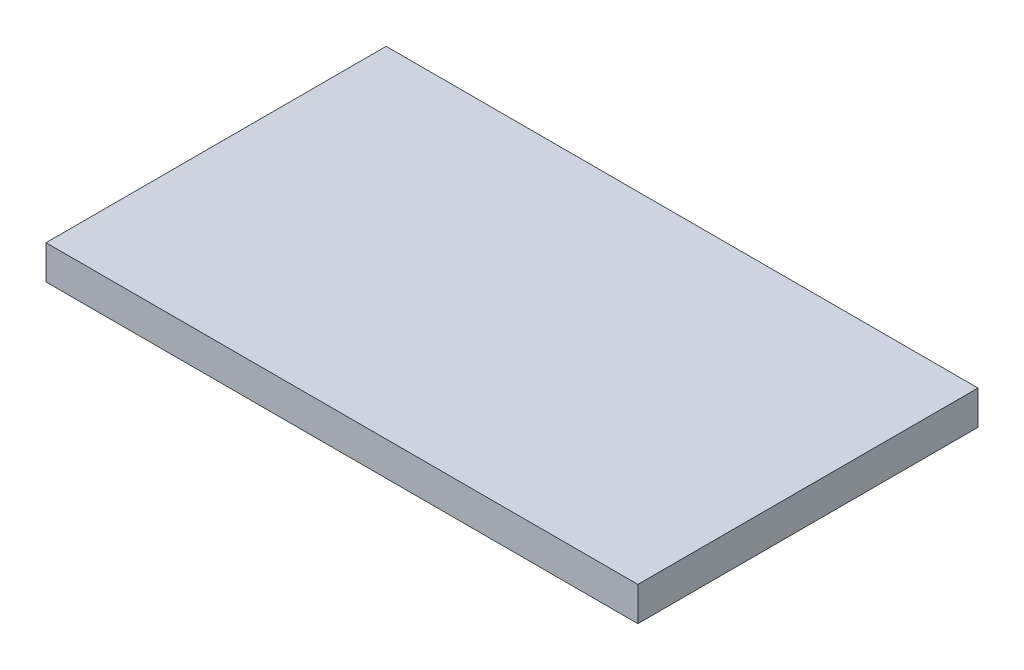
SolidWorks part; units mm, degrees
ref_plane "Front Plane" through (0, 0, 0) normal (0, 0, 1) x (1, 0, 0)
ref_plane "Top Plane" through (0, 0, 0) normal (0, 1, 0) x (1, 0, 0)
ref_plane "Right Plane" through (0, 0, 0) normal (1, 0, 0) x (0, 0, -1)
sketch "Sketch1" plane through (0, 0, 0) normal (0, 1, 0) x (1, 0, 0)
  line L1 (-43.5, 25) -> (43.5, 25)
  line L2 (-43.5, 25) -> (-43.5, -25)
  line L3 (-43.5, -25) -> (43.5, -25)
  line L4 (43.5, 25) -> (43.5, -25)
  line L5 (-43.5, 25) -> (43.5, -25) construction
  line L6 (-43.5, -25) -> (43.5, 25) construction
  point P0 (0, 0)
  dimension "D1" = 87
  dimension "D2" = 50
extrude "Boss-Extrude1" add sketch "Sketch1" along normal blind 5
